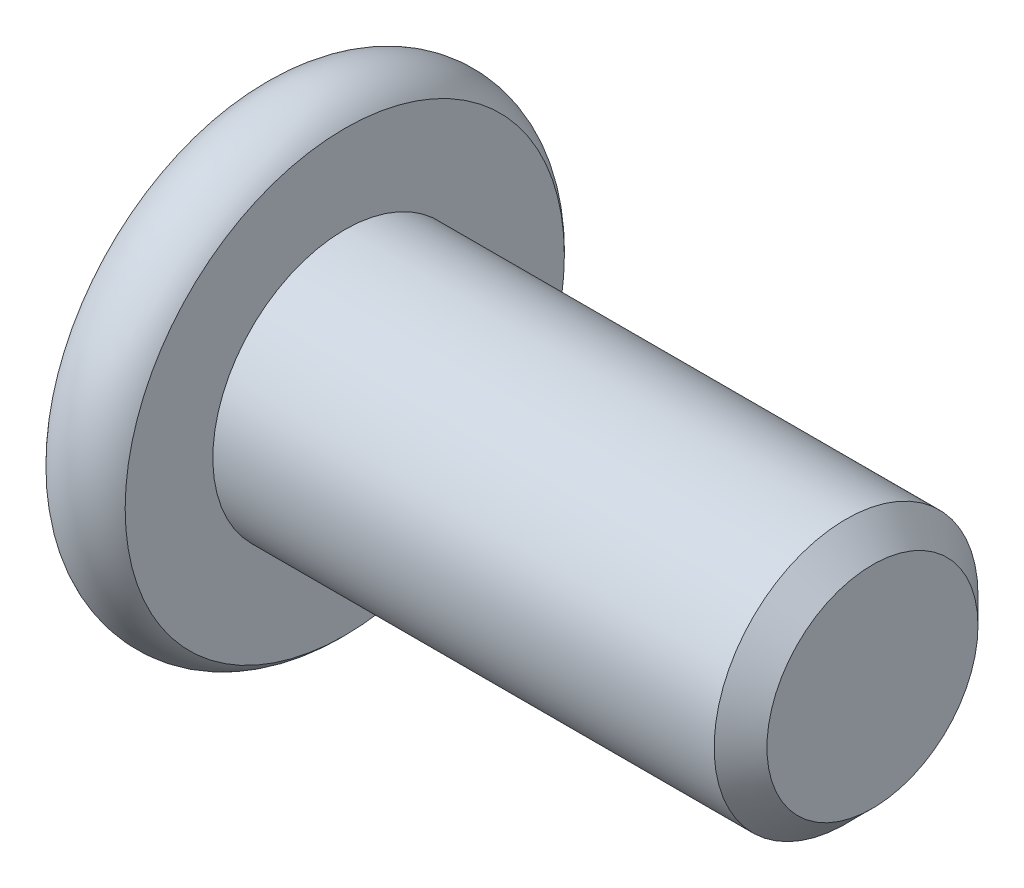
SolidWorks part; units mm, degrees
material "Plain Carbon Steel"
ref_plane "Front Plane" through (0, 0, 0) normal (0, 0, 1) x (1, 0, 0)
ref_plane "Top Plane" through (0, 0, 0) normal (0, 1, 0) x (1, 0, 0)
ref_plane "Right Plane" through (0, 0, 0) normal (1, 0, 0) x (0, 0, -1)
other "M5 x 15"
sketch "Sketch2" plane through (0, 0, 0) normal (1, 0, 0) x (0, 0, -1)
  circle A0 centre (0, 0) radius 2.5
  dimension "D1" = 5
extrude "Boss-Extrude1" add sketch "Sketch2" against normal blind 10
chamfer "Chamfer1" distance 0.5 angle 45 1 edges at (0, 0, -2.5)
sketch "Sketch6" plane through (0, 0, 0) normal (0, 0, 1) x (1, 0, 0)
  line L0 (-11.5, 0) -> (-11.5, 4.1614)
  line L1 (-11.5, 0) -> (-10, 0)
  line L2 (-10.75, 0) -> (-10.75, 3.5) construction
  line L6 (-10, 4.1614) -> (-10, 0)
  line L8 (-10, 0) -> (-14.6471, 0) construction
  line L10 (-10, 2.5) -> (-10, -2.5) construction
  arc A0 (-11.5, 4.1614) -> (-10, 4.1614) centre (-10.75, 3.5) cw
  dimension "D3" = 1
  dimension "D1" = 1.5
  dimension "D2" = 9
revolve "Revolve1" add sketch "Sketch6" angle 360 about L8
sketch "Sketch7" plane through (-11.5, 0, 0) normal (-1, 0, 0) x (0, 0, 1)
  line L1 (0, 1.7321) -> (-1.5, 0.866)
  line L2 (-1.5, 0.866) -> (-1.5, -0.866)
  line L3 (-1.5, -0.866) -> (0, -1.7321)
  line L4 (0, -1.7321) -> (1.5, -0.866)
  line L5 (1.5, -0.866) -> (1.5, 0.866)
  line L6 (1.5, 0.866) -> (0, 1.7321)
  circle A0 centre (0, 0) radius 1.5 construction
  dimension "D1" = 3
extrude "Cut-Extrude1" cut sketch "Sketch7" against normal blind 2.3
sketch "Sketch8" plane through (-11.5, 0, 0) normal (-1, 0, 0) x (0, 0, 1)
  circle A0 centre (0, 0) radius 1.7821
  dimension "D1" = 0.05
extrude "Cut-Extrude2" cut sketch "Sketch8" against normal blind 1 draft 45
